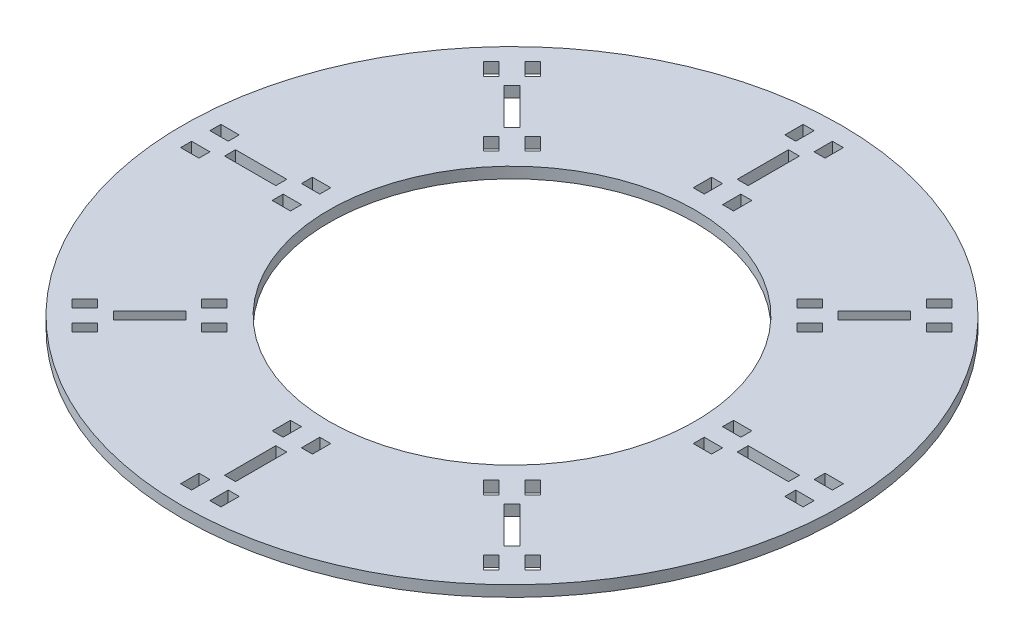
SolidWorks part; units mm, degrees
ref_plane "Front Plane" through (0, 0, 0) normal (0, 0, 1) x (1, 0, 0)
ref_plane "Top Plane" through (0, 0, 0) normal (0, 1, 0) x (1, 0, 0)
ref_plane "Right Plane" through (0, 0, 0) normal (1, 0, 0) x (0, 0, -1)
sketch "Sketch1" plane through (0, 0, 0) normal (0, 1, 0) x (1, 0, 0)
  circle A0 centre (0, 0) radius 90
  dimension "D1" = 180
extrude "Boss-Extrude1" add sketch "Sketch1" along normal blind 3
sketch "Sketch2" plane through (0, 3, 0) normal (0, 1, 0) x (1, 0, 0)
  line L1 (-1.5, 77) -> (1.5, 77)
  line L2 (-1.5, 77) -> (-1.5, 63)
  line L3 (-1.5, 63) -> (1.5, 63)
  line L4 (1.5, 77) -> (1.5, 63)
  point P4 (0, 63)
  point P6 (1.5, 70)
  dimension "D1" = 3
  dimension "D2" = 14
  dimension "D3" = 70.0161
extrude "Cut-Extrude2" cut sketch "Sketch2" against normal blind 3
sketch "Sketch15" plane through (0, 3, 0) normal (0, 1, 0) x (1, 0, 0)
  line L0 (0, 0) -> (0, 45.806) construction
pattern_circular "CirPattern1" count 8 over 360 about axis through (0, 0, 0) along (0, 1, 0) of "Cut-Extrude2"
sketch "Sketch16" plane through (0, 3, 0) normal (0, 1, 0) x (1, 0, 0)
  line L0 (-1.5, 77) -> (-1.5, 63) construction
  line L1 (-5.5, 85) -> (-2.5, 85)
  line L2 (-5.5, 85) -> (-5.5, 80)
  line L3 (-5.5, 80) -> (-2.5, 80)
  line L4 (-2.5, 85) -> (-2.5, 80)
  line L6 (2.5, 85) -> (5.5, 85)
  line L7 (2.5, 85) -> (2.5, 80)
  line L8 (2.5, 80) -> (5.5, 80)
  line L9 (5.5, 85) -> (5.5, 80)
  line L10 (-5.5, 60) -> (-2.5, 60)
  line L11 (-5.5, 60) -> (-5.5, 55)
  line L12 (-5.5, 55) -> (-2.5, 55)
  line L13 (-2.5, 60) -> (-2.5, 55)
  line L14 (2.5, 60) -> (5.5, 60)
  line L15 (2.5, 60) -> (2.5, 55)
  line L16 (2.5, 55) -> (5.5, 55)
  line L17 (5.5, 60) -> (5.5, 55)
  line L19 (1.5, 63) -> (1.5, 77) construction
  point P6 (-1.5, 70)
  point P22 (1.5, 70)
  dimension "D1" = 5
  dimension "D2" = 3
  dimension "D3" = 1
  dimension "D4" = 10
  dimension "D5" = 5
  dimension "D6" = 1
  dimension "D7" = 10
  dimension "D8" = 5
  dimension "D9" = 10
  dimension "D10" = 10
  dimension "D11" = 4
  dimension "D12" = 3
  dimension "D13" = 5
  dimension "D14" = 1
  dimension "D15" = 3
  dimension "D16" = 3
extrude "Cut-Extrude5" cut sketch "Sketch16" against normal blind 3
pattern_circular "CirPattern2" count 8 over 360 about axis through (0, 0, 0) along (0, 1, 0) of "Cut-Extrude5"
sketch "Sketch24" plane through (0, 3, 0) normal (0, 1, 0) x (1, 0, 0)
  circle A0 centre (0, 0) radius 50
  dimension "D1" = 100
extrude "Cut-Extrude6" cut sketch "Sketch24" against normal blind 3
sketch "Sketch26" plane through (0, 3, 0) normal (0, 1, 0) x (1, 0, 0)
  text T0 "B1" font "Century Gothic" height in points 22
  dimension "D1" = 4
  dimension "D2" = 67.5
